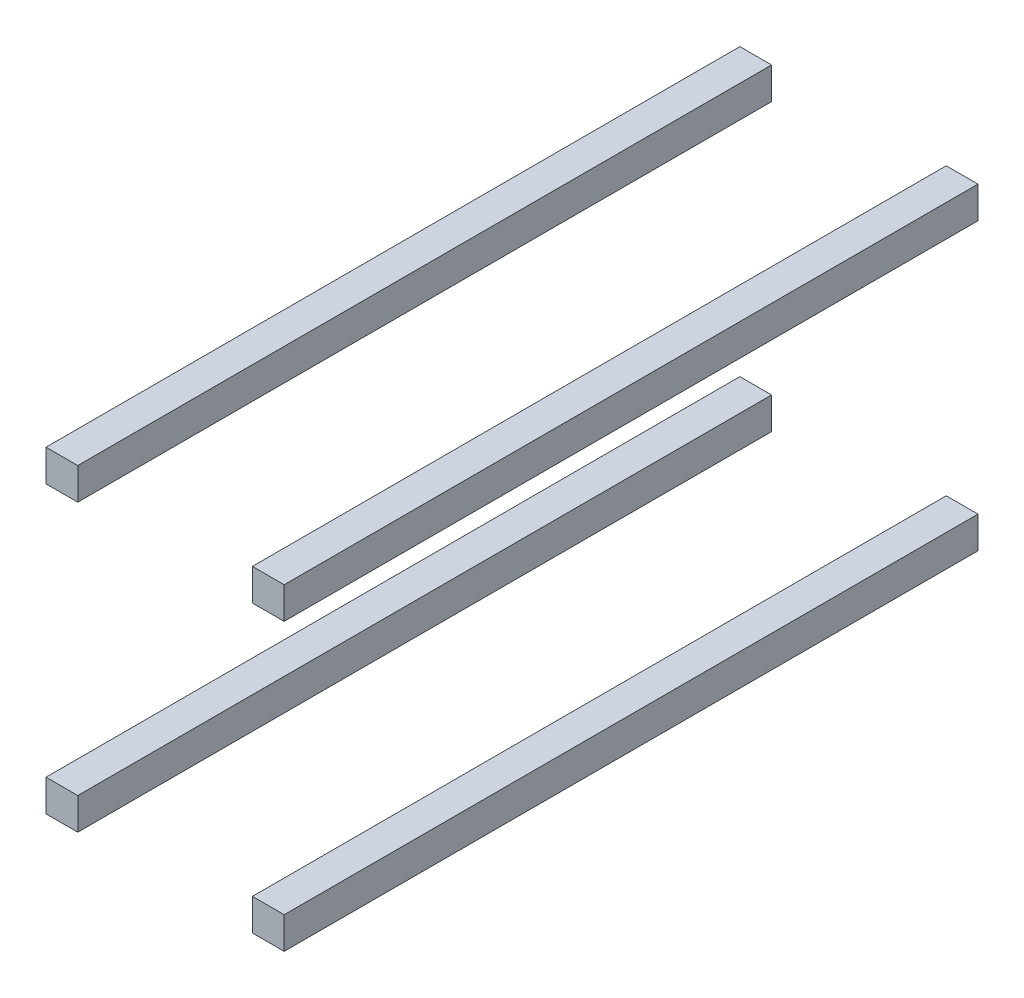
SolidWorks part; units mm, degrees
ref_plane "Front Plane" through (0, 0, 0) normal (0, 0, 1) x (1, 0, 0)
ref_plane "Top Plane" through (0, 0, 0) normal (0, 1, 0) x (1, 0, 0)
ref_plane "Right Plane" through (0, 0, 0) normal (1, 0, 0) x (0, 0, -1)
sketch "Sketch1" plane through (0, 0, 0) normal (0, 0, 1) x (1, 0, 0)
  line L1 (0, 0) -> (20, 0)
  line L2 (0, 0) -> (0, 20)
  line L3 (0, 20) -> (20, 20)
  line L4 (20, 0) -> (20, 20)
  line L5 (130, 0) -> (150, 0)
  line L6 (130, 0) -> (130, 20)
  line L7 (130, 20) -> (150, 20)
  line L8 (150, 0) -> (150, 20)
  line L9 (150, -160) -> (130, -160)
  line L10 (150, -160) -> (150, -180)
  line L11 (150, -180) -> (130, -180)
  line L12 (130, -160) -> (130, -180)
  line L13 (0, -160) -> (20, -160)
  line L14 (0, -160) -> (0, -180)
  line L15 (0, -180) -> (20, -180)
  line L16 (20, -160) -> (20, -180)
  point P17 (20, 23.602)
  point P18 (0, 0)
  point P19 (0, 0)
  point P20 (0, 0)
  point P21 (0, 0)
  dimension "D1" = 20
  dimension "D2" = 160
  dimension "D3" = 150
extrude "Boss-Extrude1" add sketch "Sketch1" along normal blind 437
